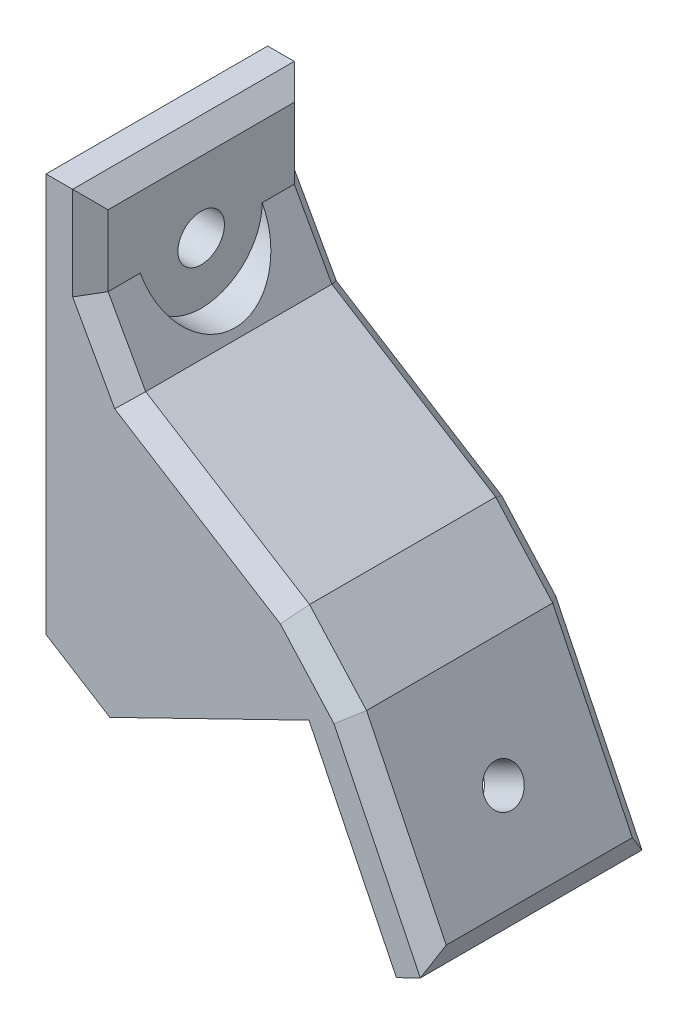
SolidWorks part; units mm, degrees
ref_plane "Plan de face" through (0, 0, 0) normal (0, 0, 1) x (1, 0, 0)
ref_plane "Plan de dessus" through (0, 0, 0) normal (0, 1, 0) x (1, 0, 0)
ref_plane "Plan de droite" through (0, 0, 0) normal (1, 0, 0) x (0, 0, -1)
sketch "Esquisse1" plane through (0, 0, 0) normal (0, 0, 1) x (1, 0, 0)
  line L0 (0, 0) -> (0, 20)
  line L1 (0, 20) -> (17.9759, 8.7674)
  line L2 (17.9759, 8.7674) -> (0, 0)
  dimension "D1" = 20
  dimension "D2" = 20
  dimension "D3" = 64
extrude "Boss.-Extru.1" add sketch "Esquisse1" along normal blind 20
sketch "Esquisse2" plane through (0, 0, 0) normal (-1, 0, 0) x (0, 0, 1)
  line L1 (0, 20) -> (20, 20)
  line L2 (0, 20) -> (0, 0)
  line L3 (0, 0) -> (20, 0)
  line L4 (20, 20) -> (20, 0)
extrude "Boss.-Extru.2" add sketch "Esquisse2" along normal blind 4
sketch "Esquisse3" plane through (0, 0, 0) normal (0.4384, -0.8988, 0) x (0.8988, 0.4384, 0)
  line L1 (0, 20) -> (20, 20)
  line L2 (0, 20) -> (0, 0)
  line L3 (0, 0) -> (20, 0)
  line L4 (20, 20) -> (20, 0)
extrude "Boss.-Extru.3" add sketch "Esquisse3" along normal blind 4
sketch "Esquisse4" plane through (0, 0, 20) normal (0, 0, 1) x (1, 0, 0)
  line L0 (-4, 20) -> (-4, 36)
  line L1 (-4, 36) -> (0, 36)
  line L2 (0, 20) -> (0, 36)
  line L3 (21.5711, 10.5209) -> (0, 24)
  line L4 (27.62, -11.006) -> (31.2152, -9.2526)
  line L5 (31.2152, -9.2526) -> (21.5711, 10.5209)
  line L6 (27.62, -11.006) -> (19.7294, 5.1722)
  line L7 (19.7294, 5.1722) -> (17.9759, 8.7674)
  line L8 (17.9759, 8.7674) -> (0, 20) construction
  line L9 (0, 20) -> (-4, 20)
  line L10 (21.5711, 10.5209) -> (17.9759, 8.7674)
  line L11 (-4, 0) -> (1.7535, -3.5952)
  line L12 (1.7535, -3.5952) -> (0, 0)
  line L13 (0, 0) -> (-4, 0)
  line M4 (19.7294, 5.1722) -> (17.9759, 8.7674)
  line M5 (17.9759, 8.7674) -> (0, 20)
  line M6 (0, 20) -> (-4, 20)
  dimension "D1" = 16
  dimension "D2" = 18
  dimension "D3" = 4
  dimension "D4" = 4
extrude "Boss.-Extru.4" add sketch "Esquisse4" against normal blind 20 contours L2 L1 L0 M6 | L10 L3 L2 M5 | L5 L10 L6 L4 M4 | L13 L11 L12
chamfer "Chanfrein1" distance 4 distance2 4 2 edges at (0, 24, 10) (21.5711, 10.5209, 10)
sketch "Esquisse5" plane through (-4, 0, 0) normal (-1, 0, 0) x (0, 0, 1)
  line L0 (0, 36) -> (20, 36) construction
  line L1 (0, 36) -> (0, 0) construction
  circle A0 centre (10, 28) radius 2.1
  dimension "D1" = 4.2
  dimension "D2" = 8
  dimension "D3" = 10
extrude "Enlèv. mat.-Extru.1" cut sketch "Esquisse5" against normal through all
sketch "Esquisse6" plane through (0, 0, 0) normal (1, 0, 0) x (0, 0, -1)
  circle A0 centre (-10, 28) radius 5.5
  dimension "D1" = 11
extrude "Enlèv. mat.-Extru.2" cut sketch "Esquisse6" along normal through all
hole_wizard "Dégagement #41" positions "Esquisse9" profile "Esquisse8" hole size "#4" standard "Ansi Inch"
sketch "Esquisse9" plane through (21.5711, 10.5209, 0) normal (0.8988, 0.4384, 0) x (0, 0, -1)
  line L0 (0, -22) -> (-20, -22) construction
  line L1 (0, -22) -> (0, -4) construction
  point P0 (-10, -13)
  dimension "D1" = 9
  dimension "D2" = 10
sketch "Esquisse8" plane through (27.2699, -1.1634, 10) normal (0, 0, 1) x (-0.4384, 0.8988, 0)
  line L0 (0, 0) -> (0, 11.0378)
  line L1 (0, 11.0378) -> (1.7272, 10)
  line L2 (1.7272, 10) -> (1.7272, 0)
  line L5 (1.7272, 0) -> (0, 0)
  line L10 (0, 11.0378) -> (-1.7272, 10) construction
  line L11 (0, -6.35) -> (0, 107.95) construction
  dimension "Diamètre du perçage" = 3.4544
  dimension "Profondeur du perçage" = 10
  dimension "Angle de pointe" = 118
chamfer "Chanfrein2" distance 1.6 angle 45 12 edges at (0, 32, 0) (0, 32, 20) (0, 36, 10) (1.6961, 24.9402, 0) (10.7855, 17.2605, 0) (10.7855, 17.2605, 20) (20.7517, 9.7832, 0) (27.2699, -1.1634, 0) (27.2699, -1.1634, 20) (31.2152, -9.2526, 10) (20.7517, 9.7832, 20) (1.6961, 24.9402, 20)
